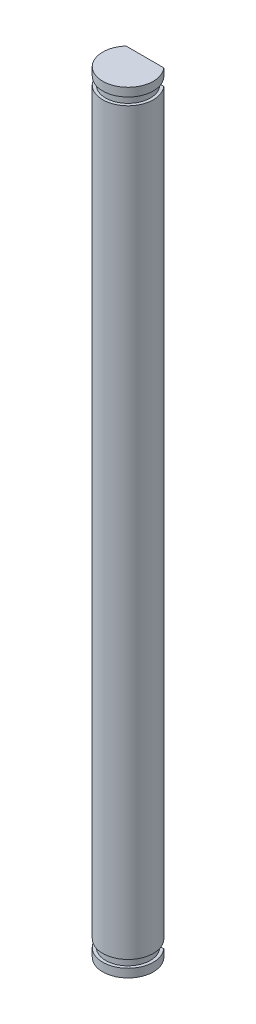
SolidWorks part; units mm, degrees
material "6061-T6 (SS)"
ref_plane "Front Plane" through (0, 0, 0) normal (0, 0, 1) x (1, 0, 0)
ref_plane "Top Plane" through (0, 0, 0) normal (0, 1, 0) x (1, 0, 0)
ref_plane "Right Plane" through (0, 0, 0) normal (1, 0, 0) x (0, 0, -1)
sketch "Sketch1" plane through (0, 0, 0) normal (0, 1, 0) x (1, 0, 0)
  line L0 (-2.2361, 2) -> (2.2361, 2)
  arc A0 (2.2361, 2) -> (-2.2361, 2) centre (0, 0) cw
  dimension "D1" = 3
  dimension "D2" = 2
extrude "Boss-Extrude1" add sketch "Sketch1" along normal mid plane 91.44
sketch "Sketch2" plane through (0, 0, 0) normal (0, 0, 1) x (1, 0, 0)
  line L8 (3, 43.82) -> (3, -43.82) construction
  line L9 (2.65, 44.72) -> (3, 44.72)
  line L10 (2.65, 44.72) -> (2.65, 43.82)
  line L11 (2.65, 43.82) -> (3, 43.82)
  line L12 (3, 44.72) -> (3, 43.82)
  line L13 (2.65, -43.82) -> (3, -43.82)
  line L14 (2.65, -43.82) -> (2.65, -44.72)
  line L15 (2.65, -44.72) -> (3, -44.72)
  line L16 (3, -43.82) -> (3, -44.72)
  line L17 (3, 45.72) -> (-3, 45.72) construction
  line L18 (0, 48.0561) -> (0, -49951.9439) construction
  point P8 (3, 0)
  dimension "D1" = 0.9
  dimension "D2" = 0.35
  dimension "D3" = 3
  dimension "D4" = 1
revolve "Cut-Revolve1" cut sketch "Sketch2" angle 360 about L18
